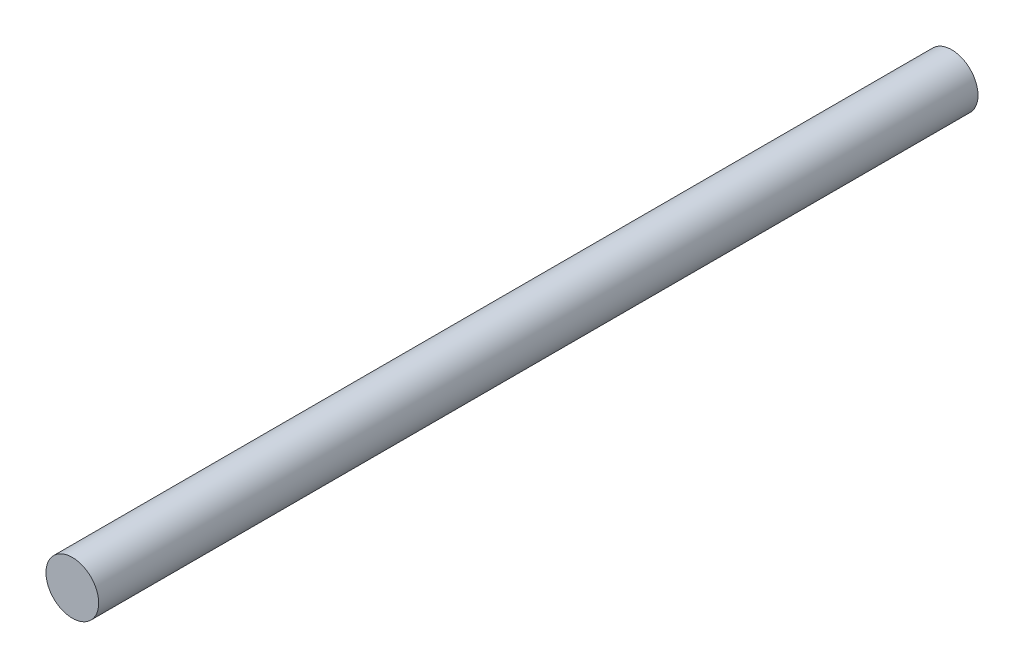
SolidWorks part; units mm, degrees
ref_plane "Front Plane" through (0, 0, 0) normal (0, 0, 1) x (1, 0, 0)
ref_plane "Top Plane" through (0, 0, 0) normal (0, 1, 0) x (1, 0, 0)
ref_plane "Right Plane" through (0, 0, 0) normal (1, 0, 0) x (0, 0, -1)
sketch "Sketch1" plane through (0, 0, 0) normal (0, 0, 1) x (1, 0, 0)
  circle A0 centre (0, 0) radius 7.5
  dimension "D1" = 15
extrude "Boss-Extrude1" add sketch "Sketch1" along normal blind 250
scale "Scale1" scale about centroid uniform scaling yes scale factor 10
scale "Scale2" scale about origin uniform scaling yes scale factor 0.75
